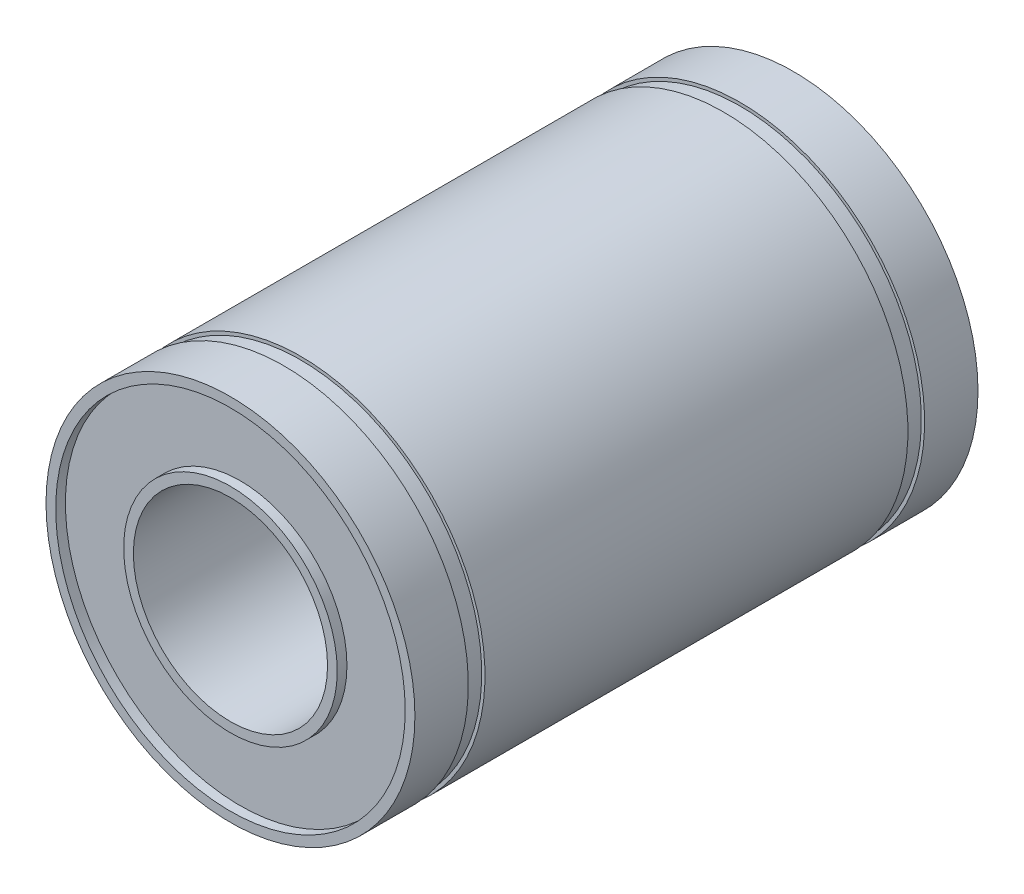
SolidWorks part; units mm, degrees
ref_plane "Front Plane" through (0, 0, 0) normal (0, 0, 1) x (1, 0, 0)
ref_plane "Top Plane" through (0, 0, 0) normal (0, 1, 0) x (1, 0, 0)
ref_plane "Right Plane" through (0, 0, 0) normal (1, 0, 0) x (0, 0, -1)
sketch "Sketch1" plane through (0, 0, 0) normal (0, 0, 1) x (1, 0, 0)
  circle A0 centre (0, 0) radius 9.5
  circle A1 centre (0, 0) radius 5
  dimension "D1" = 19
  dimension "D2" = 10
extrude "Boss-Extrude1" add sketch "Sketch1" along normal mid plane 29
sketch "Sketch2" plane through (0, 0, 0) normal (0, 1, 0) x (1, 0, 0)
  line L0 (9.5, 14.5) -> (9.5, 11.75)
  line L1 (9.5, -14.5) -> (9.5, 14.5) construction
  line L2 (9.5, 11.75) -> (9.3328, 11.75)
  line L3 (9.3328, 11.75) -> (9.3328, 10.8916)
  line L4 (9.3328, 10.8916) -> (9.5, 10.8916)
  line L5 (9.5, 10.8916) -> (9.5, 11.75)
  line L6 (0, 0) -> (14.7675, 0)
  line L7 (9.5, -10.8916) -> (9.5, -11.75)
  line L8 (9.3328, -10.8916) -> (9.5, -10.8916)
  line L9 (9.3328, -11.75) -> (9.3328, -10.8916)
  line L10 (9.5, -11.75) -> (9.3328, -11.75)
  line L11 (0, 0) -> (0, -22.6571)
  dimension "D1" = 2.75
revolve "Cut-Revolve1" cut sketch "Sketch2" angle 360 about L11
sketch "Sketch3" plane through (0, 0, 14.5) normal (0, 0, 1) x (1, 0, 0)
  circle A0 centre (0, 0) radius 9
  circle A1 centre (0, 0) radius 5 construction
  circle A2 centre (0, 0) radius 9.5
  circle A3 centre (0, 0) radius 9.5
  circle A4 centre (0, 0) radius 5
  circle A5 centre (0, 0) radius 5.5
  dimension "D1" = 0
  dimension "D2" = 0.5
  dimension "D3" = 0.5
extrude "Cut-Extrude1" cut sketch "Sketch3" against normal blind 0.5 contours A0 A5
mirror "Mirror1" about plane through (0, 0, 0) normal (0, 0, 1) of "Cut-Extrude1"
